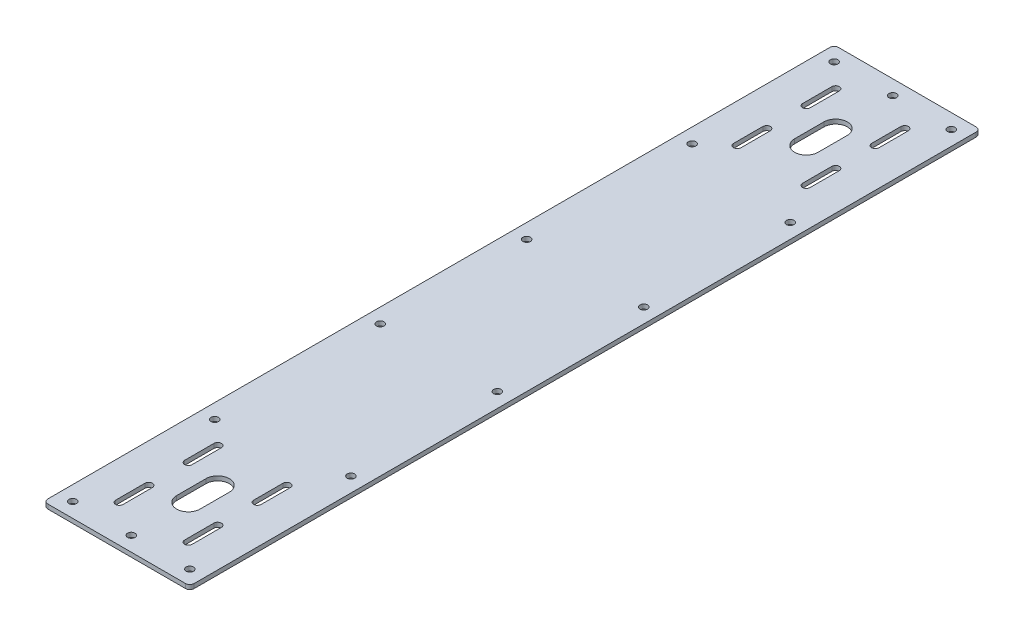
SolidWorks part; units mm, degrees
ref_plane "Front Plane" through (0, 0, 0) normal (0, 0, 1) x (1, 0, 0)
ref_plane "Top Plane" through (0, 0, 0) normal (0, 1, 0) x (1, 0, 0)
ref_plane "Right Plane" through (0, 0, 0) normal (1, 0, 0) x (0, 0, -1)
sketch "Sketch1" plane through (0, 0, 0) normal (0, 1, 0) x (1, 0, 0)
  line L0 (0, 294.8431) -> (0, -266.9671) construction
  line L1 (-47, 290) -> (47, 290)
  line L2 (-50, 287) -> (-50, -247)
  line L3 (-47, -250) -> (47, -250)
  line L4 (50, 287) -> (50, -247)
  line L7 (-80.6694, 270) -> (83.888, 270) construction
  line L8 (-73.7737, -230) -> (75.0782, -230) construction
  line L9 (-80.6694, 231) -> (83.888, 231) construction
  line L10 (0, 231) -> (51.5198, 231) construction
  line L11 (0, 285.7978) -> (0, 231) construction
  line L12 (0, 231) -> (15.5, 246.5) construction
  line L13 (14.3686, 247.6314) -> (12.3269, 245.5896) construction
  line L14 (16.6314, 245.3686) -> (14.5896, 243.3269) construction
  line L15 (-16.6314, 245.3686) -> (-14.5896, 243.3269) construction
  line L16 (-14.3686, 247.6314) -> (-12.3269, 245.5896) construction
  line L17 (-16.6314, 216.6314) -> (-14.5896, 218.6731) construction
  line L18 (-14.3686, 214.3686) -> (-12.3269, 216.4104) construction
  line L19 (16.6314, 216.6314) -> (14.5896, 218.6731) construction
  line L20 (14.3686, 214.3686) -> (12.3269, 216.4104) construction
  line L21 (-23.57, 244.57) -> (-23.57, 264.57) construction
  line L22 (-26.12, 244.57) -> (-26.12, 264.57)
  line L23 (-21.02, 244.57) -> (-21.02, 264.57)
  line L24 (23.57, 264.57) -> (23.57, 244.57) construction
  line L25 (26.12, 264.57) -> (26.12, 244.57)
  line L26 (21.02, 264.57) -> (21.02, 244.57)
  line L27 (23.57, 217.43) -> (23.57, 197.43) construction
  line L28 (26.12, 217.43) -> (26.12, 197.43)
  line L29 (21.02, 217.43) -> (21.02, 197.43)
  line L30 (-23.57, 217.43) -> (-23.57, 197.43) construction
  line L31 (-21.02, 217.43) -> (-21.02, 197.43)
  line L32 (-26.12, 217.43) -> (-26.12, 197.43)
  line L33 (-96.6445, -191) -> (75.0782, -191) construction
  line L34 (0, -191) -> (49.6455, -191) construction
  line L35 (0, -127.8353) -> (0, -191) construction
  line L36 (0, -191) -> (15.5, -175.5) construction
  line L37 (14.3686, -174.3686) -> (12.3269, -176.4104) construction
  line L38 (16.6314, -176.6314) -> (14.5896, -178.6731) construction
  line L39 (-16.6314, -176.6314) -> (-14.5896, -178.6731) construction
  line L40 (-14.3686, -174.3686) -> (-12.3269, -176.4104) construction
  line L41 (-16.6314, -205.3686) -> (-14.5896, -203.3269) construction
  line L42 (-14.3686, -207.6314) -> (-12.3269, -205.5896) construction
  line L43 (16.6314, -205.3686) -> (14.5896, -203.3269) construction
  line L44 (14.3686, -207.6314) -> (12.3269, -205.5896) construction
  line L45 (-23.57, -177.43) -> (-23.57, -157.43) construction
  line L46 (-26.12, -177.43) -> (-26.12, -157.43)
  line L47 (-21.02, -177.43) -> (-21.02, -157.43)
  line L48 (23.57, -157.43) -> (23.57, -177.43) construction
  line L49 (26.12, -157.43) -> (26.12, -177.43)
  line L50 (21.02, -157.43) -> (21.02, -177.43)
  line L51 (23.57, -204.57) -> (23.57, -224.57) construction
  line L52 (26.12, -204.57) -> (26.12, -224.57)
  line L53 (21.02, -204.57) -> (21.02, -224.57)
  line L54 (-23.57, -204.57) -> (-23.57, -224.57) construction
  line L55 (-21.02, -204.57) -> (-21.02, -224.57)
  line L56 (-26.12, -204.57) -> (-26.12, -224.57)
  line L57 (0, 241) -> (0, 221) construction
  line L58 (8, 241) -> (8, 221)
  line L59 (-8, 241) -> (-8, 221)
  line L60 (0, -181) -> (0, -201) construction
  line L61 (8, -181) -> (8, -201)
  line L62 (-8, -181) -> (-8, -201)
  arc A0 (-50, -247) -> (-47, -250) centre (-47, -247) ccw
  arc A1 (47, -250) -> (50, -247) centre (47, -247) ccw
  arc A2 (50, 287) -> (47, 290) centre (47, 287) ccw
  arc A3 (-50, 287) -> (-47, 290) centre (-47, 287) cw
  circle A4 centre (-40, 280) radius 2.55
  circle A5 centre (0, 280) radius 2.55
  circle A6 centre (40, 280) radius 2.55
  circle A7 centre (-40, -240) radius 2.55
  circle A8 centre (0, -240) radius 2.55
  circle A9 centre (40, -240) radius 2.55
  circle A10 centre (-23.57, 254.57) radius 2.55 construction
  circle A11 centre (23.57, 254.57) radius 2.55 construction
  circle A12 centre (23.57, 207.43) radius 2.55 construction
  circle A13 centre (-23.57, 207.43) radius 2.55 construction
  arc A14 (12.3269, 245.5896) -> (-12.3269, 245.5896) centre (0, 231) ccw construction
  arc A15 (-14.3686, 247.6314) -> (-16.6314, 245.3686) centre (-15.5, 246.5) ccw construction
  arc A16 (14.3686, 247.6314) -> (16.6314, 245.3686) centre (15.5, 246.5) cw construction
  arc A17 (14.3686, 214.3686) -> (16.6314, 216.6314) centre (15.5, 215.5) ccw construction
  arc A18 (-14.3686, 214.3686) -> (-16.6314, 216.6314) centre (-15.5, 215.5) cw construction
  arc A19 (-14.5896, 243.3269) -> (-14.5896, 218.6731) centre (0, 231) ccw construction
  arc A20 (-12.3269, 216.4104) -> (12.3269, 216.4104) centre (0, 231) ccw construction
  arc A21 (14.5896, 218.6731) -> (14.5896, 243.3269) centre (0, 231) ccw construction
  arc A22 (-26.12, 244.57) -> (-21.02, 244.57) centre (-23.57, 244.57) ccw
  arc A23 (-21.02, 264.57) -> (-26.12, 264.57) centre (-23.57, 264.57) ccw
  arc A24 (26.12, 264.57) -> (21.02, 264.57) centre (23.57, 264.57) ccw
  arc A25 (21.02, 244.57) -> (26.12, 244.57) centre (23.57, 244.57) ccw
  arc A26 (26.12, 217.43) -> (21.02, 217.43) centre (23.57, 217.43) ccw
  arc A27 (21.02, 197.43) -> (26.12, 197.43) centre (23.57, 197.43) ccw
  arc A28 (-21.02, 217.43) -> (-26.12, 217.43) centre (-23.57, 217.43) ccw
  arc A29 (-26.12, 197.43) -> (-21.02, 197.43) centre (-23.57, 197.43) ccw
  circle A30 centre (-23.57, -167.43) radius 2.55 construction
  circle A31 centre (23.57, -167.43) radius 2.55 construction
  circle A32 centre (23.57, -214.57) radius 2.55 construction
  circle A33 centre (-23.57, -214.57) radius 2.55 construction
  arc A34 (12.3269, -176.4104) -> (-12.3269, -176.4104) centre (0, -191) ccw construction
  arc A35 (-14.3686, -174.3686) -> (-16.6314, -176.6314) centre (-15.5, -175.5) ccw construction
  arc A36 (14.3686, -174.3686) -> (16.6314, -176.6314) centre (15.5, -175.5) cw construction
  arc A37 (14.3686, -207.6314) -> (16.6314, -205.3686) centre (15.5, -206.5) ccw construction
  arc A38 (-14.3686, -207.6314) -> (-16.6314, -205.3686) centre (-15.5, -206.5) cw construction
  arc A39 (-14.5896, -178.6731) -> (-14.5896, -203.3269) centre (0, -191) ccw construction
  arc A40 (-12.3269, -205.5896) -> (12.3269, -205.5896) centre (0, -191) ccw construction
  arc A41 (14.5896, -203.3269) -> (14.5896, -178.6731) centre (0, -191) ccw construction
  arc A42 (-26.12, -177.43) -> (-21.02, -177.43) centre (-23.57, -177.43) ccw
  arc A43 (-21.02, -157.43) -> (-26.12, -157.43) centre (-23.57, -157.43) ccw
  arc A44 (26.12, -157.43) -> (21.02, -157.43) centre (23.57, -157.43) ccw
  arc A45 (21.02, -177.43) -> (26.12, -177.43) centre (23.57, -177.43) ccw
  arc A46 (26.12, -204.57) -> (21.02, -204.57) centre (23.57, -204.57) ccw
  arc A47 (21.02, -224.57) -> (26.12, -224.57) centre (23.57, -224.57) ccw
  arc A48 (-21.02, -204.57) -> (-26.12, -204.57) centre (-23.57, -204.57) ccw
  arc A49 (-26.12, -224.57) -> (-21.02, -224.57) centre (-23.57, -224.57) ccw
  arc A50 (8, -181) -> (-8, -181) centre (0, -181) ccw
  arc A51 (8, 241) -> (-8, 241) centre (0, 241) ccw
  arc A52 (-8, 221) -> (8, 221) centre (0, 221) ccw
  arc A53 (-8, -201) -> (8, -201) centre (0, -201) ccw
  circle A54 centre (-40, 183) radius 2.55
  circle A55 centre (-40, 70) radius 2.55
  circle A56 centre (-40, -30) radius 2.55
  circle A57 centre (-40, -143) radius 2.55
  circle A58 centre (40, 170) radius 2.55
  circle A59 centre (40, 70) radius 2.55
  circle A60 centre (40, -30) radius 2.55
  circle A61 centre (40, -130) radius 2.55
  point P0 (0, 0)
  point P71 (-23.57, 254.57)
  point P77 (23.57, 254.57)
  point P85 (23.57, 207.43)
  point P91 (-23.57, 207.43)
  point P132 (-23.57, -167.43)
  point P138 (23.57, -167.43)
  point P146 (23.57, -214.57)
  point P152 (-23.57, -214.57)
  point P161 (0, 231)
  point P167 (0, -191)
  dimension "D3" = 3
  dimension "D4" = 20
  dimension "D5" = 20
  dimension "D6" = 39
  dimension "D7" = 10
  dimension "D2" = 100
  dimension "D8" = 10
  dimension "D9" = 10
  dimension "D10" = 10
  dimension "D13" = 10
  dimension "D14" = 10
  dimension "D16" = 47.14
  dimension "D17" = 47.14
  dimension "D19" = 3.2
  dimension "D20" = 45
  dimension "D21" = 31
  dimension "D22" = 39
  dimension "D11" = 10
  dimension "D12" = 10
  dimension "D23" = 5.1
  dimension "D24" = 47.14
  dimension "D25" = 47.14
  dimension "D26" = 38.2
  dimension "D27" = 3.2
  dimension "D28" = 45
  dimension "D18" = 38.2
  dimension "D15" = 5.1
  dimension "D30" = 10
  dimension "D31" = 540
  dimension "D32" = 113
  dimension "D33" = 100
  dimension "D34" = 10
  dimension "D35" = 113
  dimension "D36" = 2.55
  dimension "D37" = 5.1
  dimension "D38" = 5.1
  dimension "D39" = 8
  dimension "D40" = 16
  dimension "D29" = 31
extrude "Boss-Extrude1" add sketch "Sketch1" along normal blind 3
sketch "Sketch2" plane through (0, 0, 0) normal (0, 1, 0) x (1, 0, 0)
  line L0 (0, -181) -> (0, -201)
  line L1 (0, 241) -> (0, 221)
